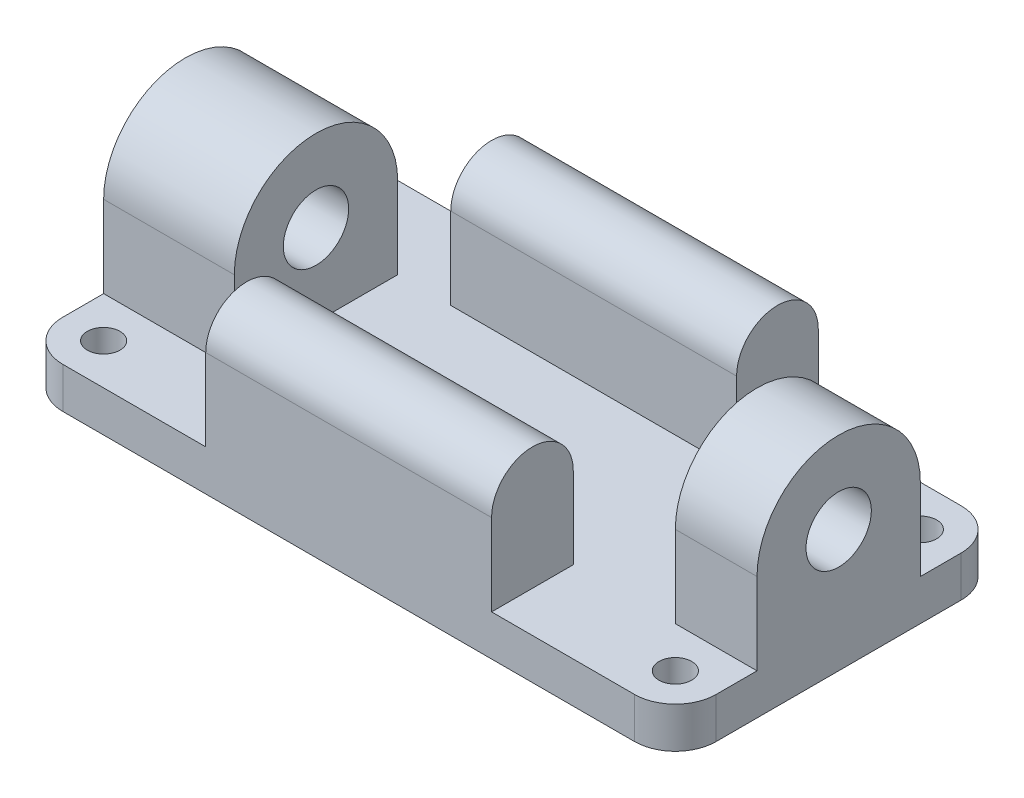
SolidWorks part; units mm, degrees
ref_plane "Ön Düzlem" through (0, 0, 0) normal (0, 0, 1) x (1, 0, 0)
ref_plane "Üst Düzlem" through (0, 0, 0) normal (0, 1, 0) x (1, 0, 0)
ref_plane "Sağ Düzlem" through (0, 0, 0) normal (1, 0, 0) x (0, 0, -1)
sketch "Sketch1" plane through (0, 0, 0) normal (0, 1, 0) x (1, 0, 0)
  line L0 (0, 0.5566) -> (0, -11.3173) construction
  line L1 (-35, 20) -> (35, 20)
  line L2 (-40, 15) -> (-40, -15)
  line L3 (-35, -20) -> (35, -20)
  line L4 (40, 15) -> (40, -15)
  line L5 (-40, 20) -> (40, -20) construction
  line L6 (-40, -20) -> (40, 20) construction
  line L7 (0, 0) -> (7.8664, 0) construction
  arc A0 (-35, 20) -> (-40, 15) centre (-35, 15) ccw
  arc A1 (40, 15) -> (35, 20) centre (35, 15) ccw
  arc A2 (35, -20) -> (40, -15) centre (35, -15) ccw
  arc A3 (-35, -20) -> (-40, -15) centre (-35, -15) cw
  circle A4 centre (-35, 15) radius 2
  circle A5 centre (-35, -15) radius 2
  circle A6 centre (35, 15) radius 2
  circle A7 centre (35, -15) radius 2
  point P0 (0, 0)
  dimension "D4" = 5
  dimension "D5" = 4
  dimension "D1" = 40
  dimension "D2" = 80
extrude "Boss-Extrude1" add sketch "Sketch1" along normal blind 5
sketch "Sketch2" plane through (40, 0, 0) normal (1, 0, 0) x (0, 0, -1)
  line L1 (0, 11.7041) -> (0, 15)
  line L2 (-10, 15) -> (-10, 0)
  line L3 (-15, 0) -> (15, 0) construction
  line L4 (-10, 0) -> (10, 0)
  line L5 (10, 0) -> (10, 15)
  line L6 (0, 11.7041) -> (0, 15)
  arc A0 (10, 15) -> (-10, 15) centre (0, 15) ccw
  dimension "D2" = 20
extrude "Boss-Extrude2" add sketch "Sketch2" against normal blind 10
sketch "Sketch3" plane through (40, 0, 0) normal (1, 0, 0) x (0, 0, -1)
  circle A0 centre (0, 15) radius 4
  dimension "D1" = 8
extrude "Cut-Extrude1" cut sketch "Sketch3" against normal blind 16
sketch "Sketch4" plane through (-40, 0, 0) normal (-1, 0, 0) x (0, 0, 1)
  line L0 (0, 0) -> (-10, 0)
  line L1 (-15, 0) -> (15, 0) construction
  line L2 (-10, 0) -> (-10, 15)
  line L4 (10, 15) -> (10, 0)
  line L5 (10, 0) -> (0, 0)
  arc A0 (10, 15) -> (-10, 15) centre (0, 15) ccw
extrude "Boss-Extrude3" add sketch "Sketch4" against normal blind 16
sketch "Sketch5" plane through (-40, 0, 0) normal (-1, 0, 0) x (0, 0, 1)
  circle A0 centre (0, 15) radius 4
  dimension "D1" = 8
extrude "Cut-Extrude2" cut sketch "Sketch5" against normal blind 23
sketch "Sketch7" plane through (0, 5, 0) normal (0, 1, 0) x (1, 0, 0)
  line L0 (35, 20) -> (-35, 20) construction
  line L1 (-17.5, 20) -> (17.5, 20)
  line L2 (-17.5, 20) -> (-17.5, 10)
  line L3 (-17.5, 10) -> (17.5, 10)
  line L4 (17.5, 20) -> (17.5, 10)
  line L5 (40, 10) -> (40, 15) construction
  dimension "D1" = 22.5
  dimension "D2" = 57.5
  dimension "D3" = 10
extrude "Boss-Extrude4" add sketch "Sketch7" along normal blind 10
sketch "Sketch8" plane through (-17.5, 0, 0) normal (-1, 0, 0) x (0, 0, 1)
  line L0 (-20, 15) -> (-10, 15) construction
  line L1 (-20, 15) -> (-10, 15)
  arc A0 (-10, 15) -> (-20, 15) centre (-15, 15) ccw
extrude "Boss-Extrude5" add sketch "Sketch8" against normal blind 35
sketch "Sketch10" plane through (0, 5, 0) normal (0, 1, 0) x (1, 0, 0)
  line L0 (-35, -20) -> (35, -20) construction
  line L1 (-17.5, -20) -> (17.5, -20)
  line L2 (-17.5, -20) -> (-17.5, -10)
  line L3 (-17.5, -10) -> (17.5, -10)
  line L4 (17.5, -20) -> (17.5, -10)
  dimension "D1" = 10
extrude "Boss-Extrude6" add sketch "Sketch10" along normal blind 10
sketch "Sketch11" plane through (17.5, 0, 0) normal (1, 0, 0) x (0, 0, -1)
  line L0 (-20, 15) -> (-10, 15) construction
  line L1 (-20, 15) -> (-10, 15)
  arc A0 (-10, 15) -> (-20, 15) centre (-15, 15) ccw
extrude "Boss-Extrude7" add sketch "Sketch11" against normal blind 35
